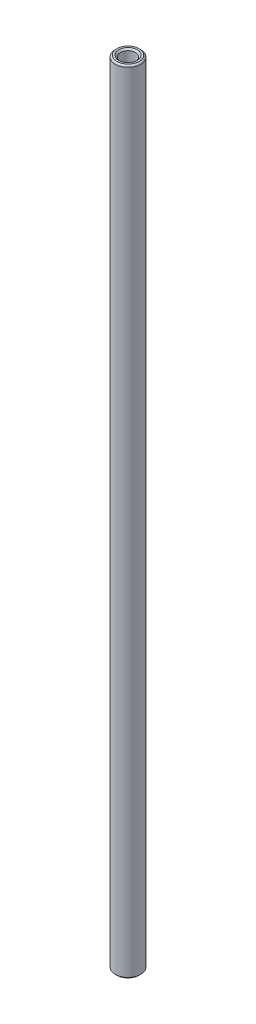
SolidWorks part; units mm, degrees
ref_plane "Front Plane" through (0, 0, 0) normal (0, 0, 1) x (1, 0, 0)
ref_plane "Top Plane" through (0, 0, 0) normal (0, 1, 0) x (1, 0, 0)
ref_plane "Right Plane" through (0, 0, 0) normal (1, 0, 0) x (0, 0, -1)
sketch "Sketch1" plane through (0, 0, 0) normal (0, 1, 0) x (1, 0, 0)
  circle A0 centre (0, 0) radius 1.9844
  circle A1 centre (0, 0) radius 1.1906
  dimension "D1" = 3.9688
  dimension "D2" = 0.7937
extrude "Boss-Extrude1" add sketch "Sketch1" along normal mid plane 123.825
chamfer "Chamfer1" distance 0.254 angle 45 4 edges at (0, -61.9125, 1.1906) (0, -61.9125, 1.9844) (0, 61.9125, 1.1906) (0, 61.9125, 1.9844)
